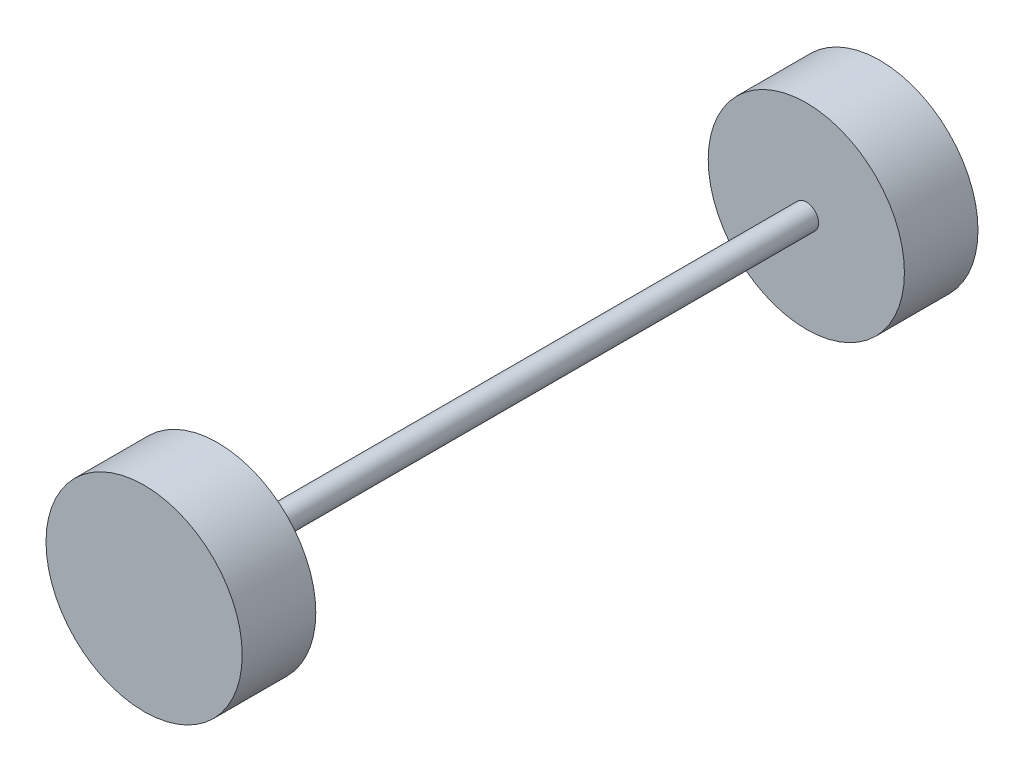
SolidWorks part; units mm, degrees
ref_plane "Front Plane" through (0, 0, 0) normal (0, 0, 1) x (1, 0, 0)
ref_plane "Top Plane" through (0, 0, 0) normal (0, 1, 0) x (1, 0, 0)
ref_plane "Right Plane" through (0, 0, 0) normal (1, 0, 0) x (0, 0, -1)
sketch "Sketch1" plane through (0, 0, 0) normal (0, 0, 1) x (1, 0, 0)
  circle A0 centre (0, 0) radius 101.6
  dimension "D1" = 203.2
extrude "Boss-Extrude1" add sketch "Sketch1" along normal blind 76.2
sketch "Sketch2" plane through (0, 0, 76.2) normal (0, 0, 1) x (1, 0, 0)
  circle A0 centre (0, 0) radius 12.7
  dimension "D1" = 25.4
extrude "Boss-Extrude2" add sketch "Sketch2" along normal blind 609.6
ref_plane "Plane4" through (0, 0, 381) normal (0, 0, 1) x (1, 0, 0)
mirror "Mirror1" about plane through (0, 0, 381) normal (0, 0, 1) of "Boss-Extrude1"
